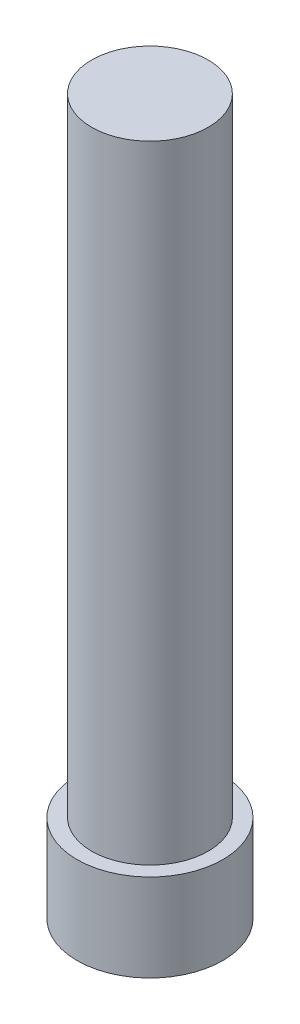
SolidWorks part; units mm, degrees
ref_plane "Front Plane" through (0, 0, 0) normal (0, 0, 1) x (1, 0, 0)
ref_plane "Top Plane" through (0, 0, 0) normal (0, 1, 0) x (1, 0, 0)
ref_plane "Right Plane" through (0, 0, 0) normal (1, 0, 0) x (0, 0, -1)
sketch "Sketch1" plane through (0, 0, 0) normal (0, 1, 0) x (1, 0, 0)
  circle A0 centre (0, 0) radius 5
extrude "Boss-Extrude1" add sketch "Sketch1" along normal blind 6
sketch "Sketch2" plane through (0, 6, 0) normal (0, 1, 0) x (1, 0, 0)
  circle A0 centre (0, 0) radius 4
extrude "Boss-Extrude2" add sketch "Sketch2" along normal blind 43
sketch "Sketch3" plane through (0, 0, 0) normal (0, -1, 0) x (1, 0, 0)
  line L1 (3.4641, 0) -> (1.7321, 3)
  line L2 (1.7321, 3) -> (-1.7321, 3)
  line L3 (-1.7321, 3) -> (-3.4641, 0)
  line L4 (-3.4641, 0) -> (-1.7321, -3)
  line L5 (-1.7321, -3) -> (1.7321, -3)
  line L6 (1.7321, -3) -> (3.4641, 0)
  circle A0 centre (0, 0) radius 3 construction
extrude "Cut-Extrude1" cut sketch "Sketch3" against normal blind 3.5
